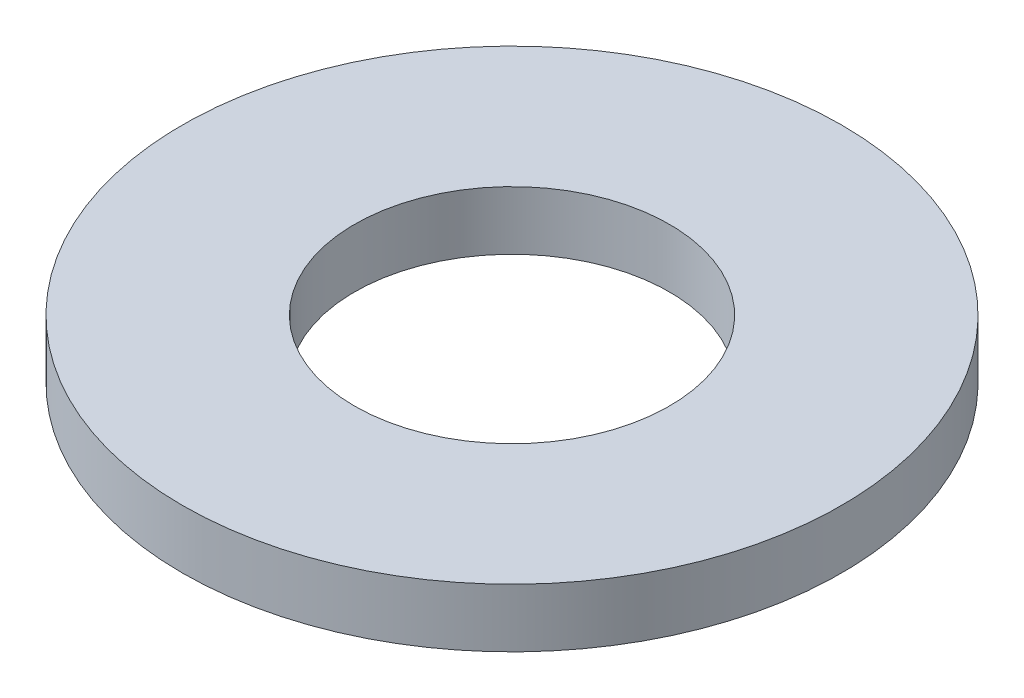
SolidWorks part; units mm, degrees
material "Plain Carbon Steel"
ref_plane "Front Plane" through (0, 0, 0) normal (0, 0, 1) x (1, 0, 0)
ref_plane "Top Plane" through (0, 0, 0) normal (0, 1, 0) x (1, 0, 0)
ref_plane "Right Plane" through (0, 0, 0) normal (1, 0, 0) x (0, 0, -1)
sketch "Sketch1" plane through (0, 0, 0) normal (0, 1, 0) x (1, 0, 0)
  circle A0 centre (0, 0) radius 2.15
  circle A1 centre (0, 0) radius 4.5
  dimension "D1" = 4.3
  dimension "D2" = 9
extrude "Extrude1" add sketch "Sketch1" along normal blind 0.8
